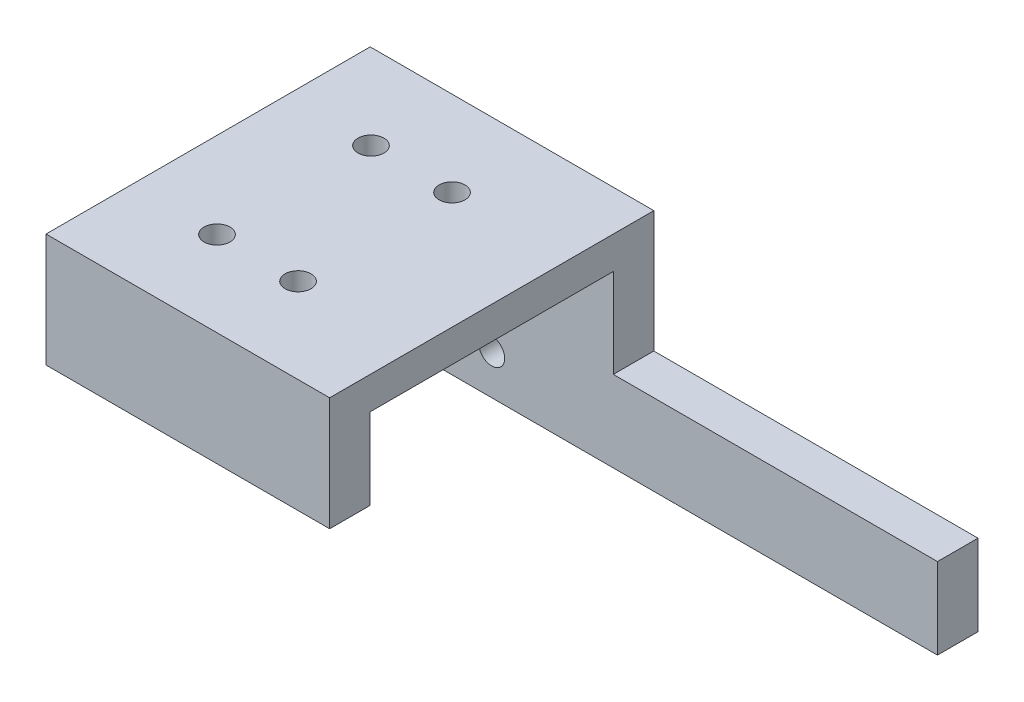
SolidWorks part; units mm, degrees
ref_plane "前视基准面" through (0, 0, 0) normal (0, 0, 1) x (1, 0, 0)
ref_plane "上视基准面" through (0, 0, 0) normal (0, 1, 0) x (1, 0, 0)
ref_plane "右视基准面" through (0, 0, 0) normal (1, 0, 0) x (0, 0, -1)
sketch "草图1" plane through (0, 0, 0) normal (0, 1, 0) x (1, 0, 0)
  line L1 (0, 0) -> (35, 0)
  line L2 (0, 0) -> (0, 40)
  line L3 (0, 40) -> (35, 40)
  line L4 (35, 0) -> (35, 40)
  dimension "D1" = 40
  dimension "D2" = 35
extrude "凸台-拉伸1" add sketch "草图1" along normal blind 4
sketch "草图2" plane through (0, 4, 0) normal (0, 1, 0) x (1, 0, 0)
  line L0 (0, 0) -> (35, 0) construction
  line L3 (0, 20) -> (35, 20) construction
  line L4 (0, 40) -> (0, 0) construction
  line L5 (35, 0) -> (35, 40) construction
  circle A0 centre (10.6, 29.5) radius 1.6
  circle A1 centre (20.6, 29.5) radius 1.6
  circle A2 centre (20.6, 10.5) radius 1.6
  circle A3 centre (10.6, 10.5) radius 1.6
  dimension "D3" = 3.2
  dimension "D1" = 10.6
  dimension "D2" = 9.5
  dimension "D4" = 10
extrude "切除-拉伸1" cut sketch "草图2" against normal blind 6
sketch "草图3" plane through (0, 0, 0) normal (0, -1, 0) x (1, 0, 0)
  line L11 (0, -40) -> (35, -40)
  line L12 (0, -40) -> (0, -35)
  line L13 (0, -35) -> (35, -35)
  line L14 (35, -40) -> (35, -35)
  dimension "D1" = 5
  dimension "D2" = 35
extrude "凸台-拉伸2" add sketch "草图3" along normal blind 21
sketch "草图4" plane through (0, 0, -40) normal (0, 0, -1) x (-1, 0, 0)
  line L1 (0, -21) -> (-35, -21) construction
  line L2 (0, 4) -> (0, -21) construction
  circle A0 centre (-10, -16) radius 1.6
  circle A1 centre (-20, -16) radius 1.6
  dimension "D1" = 3.2
  dimension "D4" = 3.2
  dimension "D2" = 10
  dimension "D3" = 5
  dimension "D5" = 5
  dimension "D6" = 10
extrude "切除-拉伸2" cut sketch "草图4" against normal blind 15
sketch "草图5" plane through (0, 0, -40) normal (0, 0, -1) x (-1, 0, 0)
  circle A0 centre (-20, -16) radius 2.8
  circle A1 centre (-10, -16) radius 2.8
  dimension "D1" = 5.6
  dimension "D2" = 5.6
extrude "切除-拉伸3" cut sketch "草图5" against normal blind 2
sketch "草图6" plane through (0, 0, -40) normal (0, 0, -1) x (-1, 0, 0)
  line L1 (-35, -21) -> (-75, -21)
  line L2 (-35, -21) -> (-35, -11)
  line L3 (-35, -11) -> (-75, -11)
  line L4 (-75, -21) -> (-75, -11)
  dimension "D1" = 10
  dimension "D2" = 40
extrude "凸台-拉伸3" add sketch "草图6" against normal blind 5
sketch "草图7" plane through (0, 0, 0) normal (0, -1, 0) x (1, 0, 0)
  line L0 (35, 0) -> (35, -35) construction
  line L1 (0, 0) -> (35, 0)
  line L2 (0, 0) -> (0, -5)
  line L3 (0, -5) -> (35, -5)
  line L4 (35, 0) -> (35, -5)
  dimension "D1" = 5
extrude "凸台-拉伸4" add sketch "草图7" along normal blind 10
